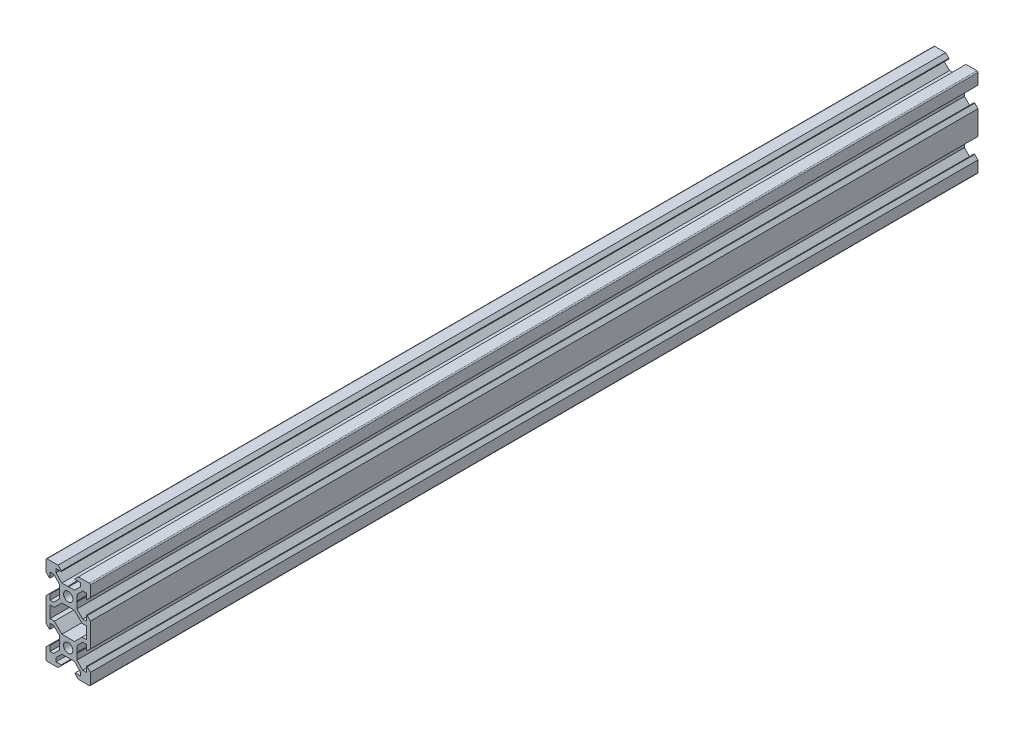
SolidWorks part; units mm, degrees
material "6061-T6 (SS)"
ref_plane "Front Plane" through (0, 0, 0) normal (0, 0, 1) x (1, 0, 0)
ref_plane "Top Plane" through (0, 0, 0) normal (0, 1, 0) x (1, 0, 0)
ref_plane "Right Plane" through (0, 0, 0) normal (1, 0, 0) x (0, 0, -1)
sketch "Sketch1" plane through (0, 0, 0) normal (0, 0, 1) x (1, 0, 0)
  line L0 (0, 0) -> (10, 0) construction
  line L1 (9.5, -20) -> (-9.5, -20)
  line L2 (10, -19.5) -> (10, 19.5)
  line L3 (9.5, 20) -> (-9.5, 20)
  line L4 (-10, -19.5) -> (-10, 19.5)
  line L5 (10, -20) -> (-10, 20) construction
  line L6 (10, 20) -> (-10, -20) construction
  circle A0 centre (0, 10) radius 2.1
  circle A1 centre (0, -10) radius 2.1
  arc A2 (-9.5, -20) -> (-10, -19.5) centre (-9.5, -19.5) cw
  arc A3 (9.5, -20) -> (10, -19.5) centre (9.5, -19.5) ccw
  arc A4 (10, 19.5) -> (9.5, 20) centre (9.5, 19.5) ccw
  arc A5 (-9.5, 20) -> (-10, 19.5) centre (-9.5, 19.5) ccw
  point P0 (0, 0)
  line B0 (0, 10) -> (0, 20) construction
  line B1 (0, 13.69) -> (-0.21, 13.9)
  line B2 (-0.21, 13.9) -> (-2.8393, 13.9)
  line B3 (-2.8393, 13.9) -> (-5.5, 16.5607)
  line B4 (-5.5, 16.5607) -> (-5.5, 18.2)
  line B5 (-5.5, 18.2) -> (-3.125, 18.2)
  line B6 (-3.125, 18.2) -> (-3.125, 18.545)
  line B7 (-3.125, 18.545) -> (-4.58, 20)
  line B8 (-4.58, 20) -> (4.58, 20)
  line B9 (0, 10) -> (-5.9132, 15.9132) construction
  line B10 (3.125, 18.545) -> (4.58, 20)
  line B11 (3.125, 18.2) -> (3.125, 18.545)
  line B12 (5.5, 18.2) -> (3.125, 18.2)
  line B13 (5.5, 16.5607) -> (5.5, 18.2)
  line B14 (2.8393, 13.9) -> (5.5, 16.5607)
  line B15 (0.21, 13.9) -> (2.8393, 13.9)
  line B16 (0, 13.69) -> (0.21, 13.9)
  line B17 (0, 10) -> (-10, 10) construction
  line B18 (-3.69, 10) -> (-3.9, 9.79)
  line B19 (-3.9, 9.79) -> (-3.9, 7.1607)
  line B20 (-3.9, 7.1607) -> (-6.5607, 4.5)
  line B21 (-6.5607, 4.5) -> (-8.2, 4.5)
  line B22 (-8.2, 4.5) -> (-8.2, 6.875)
  line B23 (-8.2, 6.875) -> (-8.545, 6.875)
  line B24 (-8.545, 6.875) -> (-10, 5.42)
  line B25 (-10, 5.42) -> (-10, 14.58)
  line B26 (0, 10) -> (-5.9132, 4.0868) construction
  line B27 (-8.545, 13.125) -> (-10, 14.58)
  line B28 (-8.2, 13.125) -> (-8.545, 13.125)
  line B29 (-8.2, 15.5) -> (-8.2, 13.125)
  line B30 (-6.5607, 15.5) -> (-8.2, 15.5)
  line B31 (-3.9, 12.8393) -> (-6.5607, 15.5)
  line B32 (-3.9, 10.21) -> (-3.9, 12.8393)
  line B33 (-3.69, 10) -> (-3.9, 10.21)
  line B34 (0, -10) -> (-10, -10) construction
  line B35 (-3.69, -10) -> (-3.9, -10.21)
  line B36 (-3.9, -10.21) -> (-3.9, -12.8393)
  line B37 (-3.9, -12.8393) -> (-6.5607, -15.5)
  line B38 (-6.5607, -15.5) -> (-8.2, -15.5)
  line B39 (-8.2, -15.5) -> (-8.2, -13.125)
  line B40 (-8.2, -13.125) -> (-8.545, -13.125)
  line B41 (-8.545, -13.125) -> (-10, -14.58)
  line B42 (-10, -14.58) -> (-10, -5.42)
  line B43 (0, -10) -> (-5.9132, -15.9132) construction
  line B44 (-8.545, -6.875) -> (-10, -5.42)
  line B45 (-8.2, -6.875) -> (-8.545, -6.875)
  line B46 (-8.2, -4.5) -> (-8.2, -6.875)
  line B47 (-6.5607, -4.5) -> (-8.2, -4.5)
  line B48 (-3.9, -7.1607) -> (-6.5607, -4.5)
  line B49 (-3.9, -9.79) -> (-3.9, -7.1607)
  line B50 (-3.69, -10) -> (-3.9, -9.79)
  line B51 (0, -10) -> (0, -20) construction
  line B52 (0, -13.69) -> (0.21, -13.9)
  line B53 (0.21, -13.9) -> (2.8393, -13.9)
  line B54 (2.8393, -13.9) -> (5.5, -16.5607)
  line B55 (5.5, -16.5607) -> (5.5, -18.2)
  line B56 (5.5, -18.2) -> (3.125, -18.2)
  line B57 (3.125, -18.2) -> (3.125, -18.545)
  line B58 (3.125, -18.545) -> (4.58, -20)
  line B59 (4.58, -20) -> (-4.58, -20)
  line B60 (0, -10) -> (5.9132, -15.9132) construction
  line B61 (-3.125, -18.545) -> (-4.58, -20)
  line B62 (-3.125, -18.2) -> (-3.125, -18.545)
  line B63 (-5.5, -18.2) -> (-3.125, -18.2)
  line B64 (-5.5, -16.5607) -> (-5.5, -18.2)
  line B65 (-2.8393, -13.9) -> (-5.5, -16.5607)
  line B66 (-0.21, -13.9) -> (-2.8393, -13.9)
  line B67 (0, -13.69) -> (-0.21, -13.9)
  line B68 (0, -10) -> (10, -10) construction
  line B69 (3.69, -10) -> (3.9, -9.79)
  line B70 (3.9, -9.79) -> (3.9, -7.1607)
  line B71 (3.9, -7.1607) -> (6.5607, -4.5)
  line B72 (6.5607, -4.5) -> (8.2, -4.5)
  line B73 (8.2, -4.5) -> (8.2, -6.875)
  line B74 (8.2, -6.875) -> (8.545, -6.875)
  line B75 (8.545, -6.875) -> (10, -5.42)
  line B76 (10, -5.42) -> (10, -14.58)
  line B77 (0, -10) -> (5.9132, -4.0868) construction
  line B78 (8.545, -13.125) -> (10, -14.58)
  line B79 (8.2, -13.125) -> (8.545, -13.125)
  line B80 (8.2, -15.5) -> (8.2, -13.125)
  line B81 (6.5607, -15.5) -> (8.2, -15.5)
  line B82 (3.9, -12.8393) -> (6.5607, -15.5)
  line B83 (3.9, -10.21) -> (3.9, -12.8393)
  line B84 (3.69, -10) -> (3.9, -10.21)
  line B85 (0, 10) -> (10, 10) construction
  line B86 (3.69, 10) -> (3.9, 10.21)
  line B87 (3.9, 10.21) -> (3.9, 12.8393)
  line B88 (3.9, 12.8393) -> (6.5607, 15.5)
  line B89 (6.5607, 15.5) -> (8.2, 15.5)
  line B90 (8.2, 15.5) -> (8.2, 13.125)
  line B91 (8.2, 13.125) -> (8.545, 13.125)
  line B92 (8.545, 13.125) -> (10, 14.58)
  line B93 (10, 14.58) -> (10, 5.42)
  line B94 (0, 10) -> (5.9132, 15.9132) construction
  line B95 (8.545, 6.875) -> (10, 5.42)
  line B96 (8.2, 6.875) -> (8.545, 6.875)
  line B97 (8.2, 4.5) -> (8.2, 6.875)
  line B98 (6.5607, 4.5) -> (8.2, 4.5)
  line B99 (3.9, 7.1607) -> (6.5607, 4.5)
  line B100 (3.9, 9.79) -> (3.9, 7.1607)
  line B101 (3.69, 10) -> (3.9, 9.79)
  line B102 (-8.2, -2.7) -> (-8.2, 2.7)
  line B103 (-8.2, 2.7) -> (-6.2393, 2.7)
  line B104 (-6.2393, 2.7) -> (-2.8393, 6.1)
  line B105 (-2.8393, 6.1) -> (2.8393, 6.1)
  line B106 (0, 6.1) -> (0, 0) construction
  line B107 (0, 0) -> (-8.2, 0) construction
  line B108 (6.2393, 2.7) -> (2.8393, 6.1)
  line B109 (8.2, 2.7) -> (6.2393, 2.7)
  line B110 (8.2, -2.7) -> (8.2, 2.7)
  line B111 (8.2, -2.7) -> (6.2393, -2.7)
  line B112 (6.2393, -2.7) -> (2.8393, -6.1)
  line B113 (-2.8393, -6.1) -> (2.8393, -6.1)
  line B114 (-6.2393, -2.7) -> (-2.8393, -6.1)
  line B115 (-8.2, -2.7) -> (-6.2393, -2.7)
  line B116 (0, 6.1) -> (0, 10) construction
  line B117 (0, 10) -> (-5.0927, 4.9073) construction
  dimension "D4" = 4.2
  dimension "D5" = 0.5
  dimension "D1" = 20
  dimension "D2" = 40
  dimension "D3" = 20
sketch_block_instance "V Slot 1-4"
sketch_block "V Slot 1" parameters "D1"=10, "D2"=11, "D3"=4.3, "D4"=1.8, "D5"=0.21, "D6"=45, "D7"=9.16, "D8"=1.5, "D9"=6.25
sketch_block_instance "V Slot 1-5"
sketch_block_instance "V Slot 1-6"
sketch_block_instance "V Slot 1-7"
sketch_block_instance "V Slot 1-8"
sketch_block_instance "V Slot 1-9"
sketch_block_instance "Center Cutout 1-1"
sketch_block "Center Cutout 1" parameters "D1"=5.4, "D2"=12.2, "D3"=8.2, "D4"=45, "D5"=10, "D6"=1.5
extrude "Boss-Extrude1" add sketch "Sketch1" along normal blind 400 contours B101 B86 B87 B88 B89 B90 B91 B92 L2 A4 L3 B10 B11 B12 B13 B14 B15 B16 B1 B2 B3 B4 B5 B6 B7 A5 L4 B27 B28 B29 B30 B31 B32 B33 B18 B19 B20 B21 B22 B23 B24 B44 B45 B46 B47 B48 B49 B50 B35
